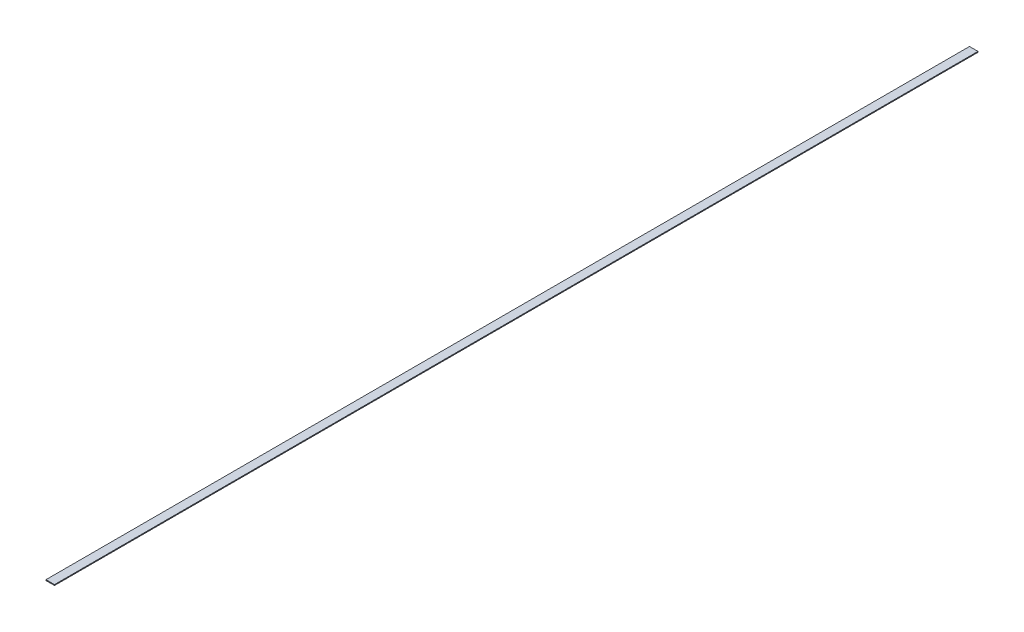
SolidWorks part; units mm, degrees
ref_plane "Front Plane" through (0, 0, 0) normal (0, 0, 1) x (1, 0, 0)
ref_plane "Top Plane" through (0, 0, 0) normal (0, 1, 0) x (1, 0, 0)
ref_plane "Right Plane" through (0, 0, 0) normal (1, 0, 0) x (0, 0, -1)
sketch "Sketch1" plane through (0, 0, 0) normal (0, 1, 0) x (1, 0, 0)
  line L1 (0, 0) -> (50.8, 0)
  line L2 (0, 0) -> (0, 5518.15)
  line L3 (0, 5518.15) -> (50.8, 5518.15)
  line L4 (50.8, 0) -> (50.8, 5518.15)
  dimension "D1" = 50.8
  dimension "D2" = 5518.15
extrude "Boss-Extrude1" add sketch "Sketch1" along normal blind 5.08
